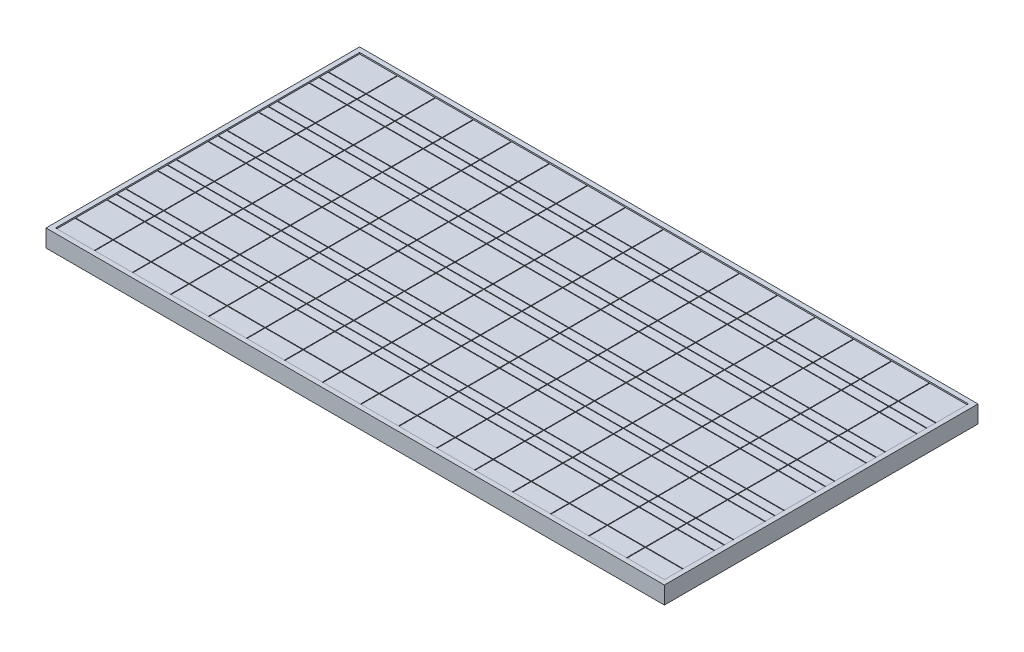
SolidWorks part; units mm, degrees
ref_plane "Front Plane" through (0, 0, 0) normal (0, 0, 1) x (1, 0, 0)
ref_plane "Top Plane" through (0, 0, 0) normal (0, 1, 0) x (1, 0, 0)
ref_plane "Right Plane" through (0, 0, 0) normal (1, 0, 0) x (0, 0, -1)
sketch "Sketch1" plane through (0, 0, 0) normal (0, 1, 0) x (1, 0, 0)
  line L1 (978, -496) -> (-978, -496)
  line L2 (978, -496) -> (978, 496)
  line L3 (978, 496) -> (-978, 496)
  line L4 (-978, -496) -> (-978, 496)
  line L5 (978, -496) -> (-978, 496) construction
  line L6 (978, 496) -> (-978, -496) construction
  line L11 (846.3925, -429.2543) -> (-845.4266, 428.7644) construction
  line L12 (846.3275, 428.1843) -> (-846.3275, -428.1843) construction
  point P0 (0, 0)
  point P6 (0, 0)
  dimension "D1" = 1956
  dimension "D2" = 992
extrude "Boss-Extrude1" add sketch "Sketch1" along normal blind 50
sketch "Sketch2" plane through (0, 0, 0) normal (0, -1, 0) x (1, 0, 0)
  line L14 (938, -456) -> (938, 456)
  line L15 (-938, -456) -> (938, -456)
  line L16 (-938, 456) -> (-938, -456)
  line L17 (938, 456) -> (-938, 456)
  line L18 (938, -456) -> (938, 456)
  line L19 (-938, -456) -> (938, -456)
  line L20 (-938, 456) -> (-938, -456)
  line L21 (938, 456) -> (-938, 456)
  dimension "D1" = 40
extrude "Cut-Extrude1" cut sketch "Sketch2" against normal blind 25
sketch "Sketch4" plane through (0, 50, 0) normal (0, 1, 0) x (1, 0, 0)
  line L13 (-963, 481) -> (-963, -481)
  line L14 (-963, -481) -> (963, -481)
  line L15 (963, -481) -> (963, 481)
  line L16 (963, 481) -> (-963, 481)
  line L17 (-963, 481) -> (-963, -481)
  line L18 (-963, -481) -> (963, -481)
  line L19 (963, -481) -> (963, 481)
  line L20 (963, 481) -> (-963, 481)
  line L21 (-978, 496) -> (-978, -496)
  line L22 (-978, -496) -> (978, -496)
  line L23 (978, -496) -> (978, 496)
  line L24 (978, 496) -> (-978, 496)
  line L25 (-978, 496) -> (-978, -496)
  line L26 (-978, -496) -> (978, -496)
  line L27 (978, -496) -> (978, 496)
  line L28 (978, 496) -> (-978, 496)
  dimension "D1" = 15
  dimension "D2" = 0
extrude "Boss-Extrude3" add sketch "Sketch4" along normal blind 5
sketch "Sketch5" plane through (0, 50, 0) normal (0, 1, 0) x (1, 0, 0)
  line L0 (-963, -481) -> (963, -481) construction
  line L1 (-961, -479) -> (-842.75, -479)
  line L2 (-961, -479) -> (-961, -421)
  line L3 (-961, -321) -> (-842.75, -321)
  line L4 (-842.75, -479) -> (-842.75, -421)
  line L5 (-963, 481) -> (-963, -481) construction
  line L6 (-961, -419) -> (-961, -321)
  line L7 (-961, -421) -> (-842.75, -421)
  line L9 (-961, -419) -> (-842.75, -419)
  line L11 (-842.75, -419) -> (-842.75, -321)
  line L12 (-961, -161) -> (-842.75, -161)
  line L13 (-842.75, -259) -> (-842.75, -161)
  line L14 (-961, -259) -> (-842.75, -259)
  line L15 (-961, -259) -> (-961, -161)
  line L16 (-961, -1) -> (-842.75, -1)
  line L17 (-842.75, -99) -> (-842.75, -1)
  line L18 (-961, -99) -> (-842.75, -99)
  line L19 (-961, -99) -> (-961, -1)
  line L20 (-961, 159) -> (-842.75, 159)
  line L21 (-842.75, 61) -> (-842.75, 159)
  line L22 (-961, 61) -> (-842.75, 61)
  line L23 (-961, 61) -> (-961, 159)
  line L24 (-961, 319) -> (-842.75, 319)
  line L25 (-842.75, 221) -> (-842.75, 319)
  line L26 (-961, 221) -> (-842.75, 221)
  line L27 (-961, 221) -> (-961, 319)
  line L28 (-961, 479) -> (-842.75, 479)
  line L29 (-842.75, 381) -> (-842.75, 479)
  line L30 (-961, 381) -> (-842.75, 381)
  line L31 (-961, 381) -> (-961, 479)
  line L32 (-961, -319) -> (-842.75, -319)
  line L33 (-842.75, -319) -> (-842.75, -290)
  line L34 (-961, -261) -> (-842.75, -261)
  line L35 (-961, -319) -> (-961, -290)
  line L36 (-961, -159) -> (-842.75, -159)
  line L37 (-842.75, -159) -> (-842.75, -130)
  line L38 (-961, -101) -> (-842.75, -101)
  line L39 (-961, -159) -> (-961, -130)
  line L40 (-961, 1) -> (-842.75, 1)
  line L41 (-842.75, 1) -> (-842.75, 30)
  line L42 (-961, 59) -> (-842.75, 59)
  line L43 (-961, 1) -> (-961, 30)
  line L44 (-961, 161) -> (-842.75, 161)
  line L45 (-842.75, 161) -> (-842.75, 190)
  line L46 (-961, 219) -> (-842.75, 219)
  line L47 (-961, 161) -> (-961, 190)
  line L48 (-961, 321) -> (-842.75, 321)
  line L49 (-842.75, 321) -> (-842.75, 350)
  line L50 (-961, 379) -> (-842.75, 379)
  line L51 (-961, 321) -> (-961, 350)
  line L53 (-961, -290) -> (-842.75, -290)
  line L55 (-961, -288) -> (-842.75, -288)
  line L57 (-961, -130) -> (-842.75, -130)
  line L59 (-961, -128) -> (-842.75, -128)
  line L61 (-961, 30) -> (-842.75, 30)
  line L63 (-961, 32) -> (-842.75, 32)
  line L65 (-961, 190) -> (-842.75, 190)
  line L67 (-961, 192) -> (-842.75, 192)
  line L69 (-961, 350) -> (-842.75, 350)
  line L71 (-961, 352) -> (-842.75, 352)
  line L72 (-961, -288) -> (-961, -261)
  line L73 (-842.75, -288) -> (-842.75, -261)
  line L74 (-961, -128) -> (-961, -101)
  line L75 (-842.75, -128) -> (-842.75, -101)
  line L76 (-961, 32) -> (-961, 59)
  line L77 (-842.75, 32) -> (-842.75, 59)
  line L78 (-961, 192) -> (-961, 219)
  line L79 (-842.75, 192) -> (-842.75, 219)
  line L80 (-961, 352) -> (-961, 379)
  line L81 (-842.75, 352) -> (-842.75, 379)
  line L82 (-840.75, -479) -> (-722.5, -479)
  line L83 (-722.5, -479) -> (-722.5, -421)
  line L84 (-840.75, -421) -> (-722.5, -421)
  line L85 (-840.75, -479) -> (-840.75, -421)
  line L86 (-840.75, -321) -> (-722.5, -321)
  line L87 (-722.5, -419) -> (-722.5, -321)
  line L88 (-840.75, -419) -> (-722.5, -419)
  line L89 (-840.75, -419) -> (-840.75, -321)
  line L90 (-840.75, -319) -> (-722.5, -319)
  line L91 (-722.5, -319) -> (-722.5, -290)
  line L92 (-840.75, -290) -> (-722.5, -290)
  line L93 (-840.75, -319) -> (-840.75, -290)
  line L94 (-840.75, -261) -> (-722.5, -261)
  line L95 (-722.5, -288) -> (-722.5, -261)
  line L96 (-840.75, -288) -> (-722.5, -288)
  line L97 (-840.75, -288) -> (-840.75, -261)
  line L98 (-840.75, -161) -> (-722.5, -161)
  line L99 (-722.5, -259) -> (-722.5, -161)
  line L100 (-840.75, -259) -> (-722.5, -259)
  line L101 (-840.75, -259) -> (-840.75, -161)
  line L102 (-840.75, -159) -> (-722.5, -159)
  line L103 (-722.5, -159) -> (-722.5, -130)
  line L104 (-840.75, -130) -> (-722.5, -130)
  line L105 (-840.75, -159) -> (-840.75, -130)
  line L106 (-840.75, -101) -> (-722.5, -101)
  line L107 (-722.5, -128) -> (-722.5, -101)
  line L108 (-840.75, -128) -> (-722.5, -128)
  line L109 (-840.75, -128) -> (-840.75, -101)
  line L110 (-840.75, -1) -> (-722.5, -1)
  line L111 (-722.5, -99) -> (-722.5, -1)
  line L112 (-840.75, -99) -> (-722.5, -99)
  line L113 (-840.75, -99) -> (-840.75, -1)
  line L114 (-840.75, 1) -> (-722.5, 1)
  line L115 (-722.5, 1) -> (-722.5, 30)
  line L116 (-840.75, 30) -> (-722.5, 30)
  line L117 (-840.75, 1) -> (-840.75, 30)
  line L118 (-840.75, 59) -> (-722.5, 59)
  line L119 (-722.5, 32) -> (-722.5, 59)
  line L120 (-840.75, 32) -> (-722.5, 32)
  line L121 (-840.75, 32) -> (-840.75, 59)
  line L122 (-840.75, 159) -> (-722.5, 159)
  line L123 (-722.5, 61) -> (-722.5, 159)
  line L124 (-840.75, 61) -> (-722.5, 61)
  line L125 (-840.75, 61) -> (-840.75, 159)
  line L126 (-840.75, 161) -> (-722.5, 161)
  line L127 (-722.5, 161) -> (-722.5, 190)
  line L128 (-840.75, 190) -> (-722.5, 190)
  line L129 (-840.75, 161) -> (-840.75, 190)
  line L130 (-840.75, 219) -> (-722.5, 219)
  line L131 (-722.5, 192) -> (-722.5, 219)
  line L132 (-840.75, 192) -> (-722.5, 192)
  line L133 (-840.75, 192) -> (-840.75, 219)
  line L134 (-840.75, 319) -> (-722.5, 319)
  line L135 (-722.5, 221) -> (-722.5, 319)
  line L136 (-840.75, 221) -> (-722.5, 221)
  line L137 (-840.75, 221) -> (-840.75, 319)
  line L138 (-840.75, 321) -> (-722.5, 321)
  line L139 (-722.5, 321) -> (-722.5, 350)
  line L140 (-840.75, 350) -> (-722.5, 350)
  line L141 (-840.75, 321) -> (-840.75, 350)
  line L142 (-840.75, 379) -> (-722.5, 379)
  line L143 (-722.5, 352) -> (-722.5, 379)
  line L144 (-840.75, 352) -> (-722.5, 352)
  line L145 (-840.75, 352) -> (-840.75, 379)
  line L146 (-840.75, 479) -> (-722.5, 479)
  line L147 (-722.5, 381) -> (-722.5, 479)
  line L148 (-840.75, 381) -> (-722.5, 381)
  line L149 (-840.75, 381) -> (-840.75, 479)
  line L150 (-720.5, -479) -> (-602.25, -479)
  line L151 (-602.25, -479) -> (-602.25, -421)
  line L152 (-720.5, -421) -> (-602.25, -421)
  line L153 (-720.5, -479) -> (-720.5, -421)
  line L154 (-720.5, -321) -> (-602.25, -321)
  line L155 (-602.25, -419) -> (-602.25, -321)
  line L156 (-720.5, -419) -> (-602.25, -419)
  line L157 (-720.5, -419) -> (-720.5, -321)
  line L158 (-720.5, -319) -> (-602.25, -319)
  line L159 (-602.25, -319) -> (-602.25, -290)
  line L160 (-720.5, -290) -> (-602.25, -290)
  line L161 (-720.5, -319) -> (-720.5, -290)
  line L162 (-720.5, -261) -> (-602.25, -261)
  line L163 (-602.25, -288) -> (-602.25, -261)
  line L164 (-720.5, -288) -> (-602.25, -288)
  line L165 (-720.5, -288) -> (-720.5, -261)
  line L166 (-720.5, -161) -> (-602.25, -161)
  line L167 (-602.25, -259) -> (-602.25, -161)
  line L168 (-720.5, -259) -> (-602.25, -259)
  line L169 (-720.5, -259) -> (-720.5, -161)
  line L170 (-720.5, -159) -> (-602.25, -159)
  line L171 (-602.25, -159) -> (-602.25, -130)
  line L172 (-720.5, -130) -> (-602.25, -130)
  line L173 (-720.5, -159) -> (-720.5, -130)
  line L174 (-720.5, -101) -> (-602.25, -101)
  line L175 (-602.25, -128) -> (-602.25, -101)
  line L176 (-720.5, -128) -> (-602.25, -128)
  line L177 (-720.5, -128) -> (-720.5, -101)
  line L178 (-720.5, -1) -> (-602.25, -1)
  line L179 (-602.25, -99) -> (-602.25, -1)
  line L180 (-720.5, -99) -> (-602.25, -99)
  line L181 (-720.5, -99) -> (-720.5, -1)
  line L182 (-720.5, 1) -> (-602.25, 1)
  line L183 (-602.25, 1) -> (-602.25, 30)
  line L184 (-720.5, 30) -> (-602.25, 30)
  line L185 (-720.5, 1) -> (-720.5, 30)
  line L186 (-720.5, 59) -> (-602.25, 59)
  line L187 (-602.25, 32) -> (-602.25, 59)
  line L188 (-720.5, 32) -> (-602.25, 32)
  line L189 (-720.5, 32) -> (-720.5, 59)
  line L190 (-720.5, 159) -> (-602.25, 159)
  line L191 (-602.25, 61) -> (-602.25, 159)
  line L192 (-720.5, 61) -> (-602.25, 61)
  line L193 (-720.5, 61) -> (-720.5, 159)
  line L194 (-720.5, 161) -> (-602.25, 161)
  line L195 (-602.25, 161) -> (-602.25, 190)
  line L196 (-720.5, 190) -> (-602.25, 190)
  line L197 (-720.5, 161) -> (-720.5, 190)
  line L198 (-720.5, 219) -> (-602.25, 219)
  line L199 (-602.25, 192) -> (-602.25, 219)
  line L200 (-720.5, 192) -> (-602.25, 192)
  line L201 (-720.5, 192) -> (-720.5, 219)
  line L202 (-720.5, 319) -> (-602.25, 319)
  line L203 (-602.25, 221) -> (-602.25, 319)
  line L204 (-720.5, 221) -> (-602.25, 221)
  line L205 (-720.5, 221) -> (-720.5, 319)
  line L206 (-720.5, 321) -> (-602.25, 321)
  line L207 (-602.25, 321) -> (-602.25, 350)
  line L208 (-720.5, 350) -> (-602.25, 350)
  line L209 (-720.5, 321) -> (-720.5, 350)
  line L210 (-720.5, 379) -> (-602.25, 379)
  line L211 (-602.25, 352) -> (-602.25, 379)
  line L212 (-720.5, 352) -> (-602.25, 352)
  line L213 (-720.5, 352) -> (-720.5, 379)
  line L214 (-720.5, 479) -> (-602.25, 479)
  line L215 (-602.25, 381) -> (-602.25, 479)
  line L216 (-720.5, 381) -> (-602.25, 381)
  line L217 (-720.5, 381) -> (-720.5, 479)
  line L218 (-600.25, -479) -> (-482, -479)
  line L219 (-482, -479) -> (-482, -421)
  line L220 (-600.25, -421) -> (-482, -421)
  line L221 (-600.25, -479) -> (-600.25, -421)
  line L222 (-600.25, -321) -> (-482, -321)
  line L223 (-482, -419) -> (-482, -321)
  line L224 (-600.25, -419) -> (-482, -419)
  line L225 (-600.25, -419) -> (-600.25, -321)
  line L226 (-600.25, -319) -> (-482, -319)
  line L227 (-482, -319) -> (-482, -290)
  line L228 (-600.25, -290) -> (-482, -290)
  line L229 (-600.25, -319) -> (-600.25, -290)
  line L230 (-600.25, -261) -> (-482, -261)
  line L231 (-482, -288) -> (-482, -261)
  line L232 (-600.25, -288) -> (-482, -288)
  line L233 (-600.25, -288) -> (-600.25, -261)
  line L234 (-600.25, -161) -> (-482, -161)
  line L235 (-482, -259) -> (-482, -161)
  line L236 (-600.25, -259) -> (-482, -259)
  line L237 (-600.25, -259) -> (-600.25, -161)
  line L238 (-600.25, -159) -> (-482, -159)
  line L239 (-482, -159) -> (-482, -130)
  line L240 (-600.25, -130) -> (-482, -130)
  line L241 (-600.25, -159) -> (-600.25, -130)
  line L242 (-600.25, -101) -> (-482, -101)
  line L243 (-482, -128) -> (-482, -101)
  line L244 (-600.25, -128) -> (-482, -128)
  line L245 (-600.25, -128) -> (-600.25, -101)
  line L246 (-600.25, -1) -> (-482, -1)
  line L247 (-482, -99) -> (-482, -1)
  line L248 (-600.25, -99) -> (-482, -99)
  line L249 (-600.25, -99) -> (-600.25, -1)
  line L250 (-600.25, 1) -> (-482, 1)
  line L251 (-482, 1) -> (-482, 30)
  line L252 (-600.25, 30) -> (-482, 30)
  line L253 (-600.25, 1) -> (-600.25, 30)
  line L254 (-600.25, 59) -> (-482, 59)
  line L255 (-482, 32) -> (-482, 59)
  line L256 (-600.25, 32) -> (-482, 32)
  line L257 (-600.25, 32) -> (-600.25, 59)
  line L258 (-600.25, 159) -> (-482, 159)
  line L259 (-482, 61) -> (-482, 159)
  line L260 (-600.25, 61) -> (-482, 61)
  line L261 (-600.25, 61) -> (-600.25, 159)
  line L262 (-600.25, 161) -> (-482, 161)
  line L263 (-482, 161) -> (-482, 190)
  line L264 (-600.25, 190) -> (-482, 190)
  line L265 (-600.25, 161) -> (-600.25, 190)
  line L266 (-600.25, 219) -> (-482, 219)
  line L267 (-482, 192) -> (-482, 219)
  line L268 (-600.25, 192) -> (-482, 192)
  line L269 (-600.25, 192) -> (-600.25, 219)
  line L270 (-600.25, 319) -> (-482, 319)
  line L271 (-482, 221) -> (-482, 319)
  line L272 (-600.25, 221) -> (-482, 221)
  line L273 (-600.25, 221) -> (-600.25, 319)
  line L274 (-600.25, 321) -> (-482, 321)
  line L275 (-482, 321) -> (-482, 350)
  line L276 (-600.25, 350) -> (-482, 350)
  line L277 (-600.25, 321) -> (-600.25, 350)
  line L278 (-600.25, 379) -> (-482, 379)
  line L279 (-482, 352) -> (-482, 379)
  line L280 (-600.25, 352) -> (-482, 352)
  line L281 (-600.25, 352) -> (-600.25, 379)
  line L282 (-600.25, 479) -> (-482, 479)
  line L283 (-482, 381) -> (-482, 479)
  line L284 (-600.25, 381) -> (-482, 381)
  line L285 (-600.25, 381) -> (-600.25, 479)
  line L286 (-480, -479) -> (-361.75, -479)
  line L287 (-361.75, -479) -> (-361.75, -421)
  line L288 (-480, -421) -> (-361.75, -421)
  line L289 (-480, -479) -> (-480, -421)
  line L290 (-480, -321) -> (-361.75, -321)
  line L291 (-361.75, -419) -> (-361.75, -321)
  line L292 (-480, -419) -> (-361.75, -419)
  line L293 (-480, -419) -> (-480, -321)
  line L294 (-480, -319) -> (-361.75, -319)
  line L295 (-361.75, -319) -> (-361.75, -290)
  line L296 (-480, -290) -> (-361.75, -290)
  line L297 (-480, -319) -> (-480, -290)
  line L298 (-480, -261) -> (-361.75, -261)
  line L299 (-361.75, -288) -> (-361.75, -261)
  line L300 (-480, -288) -> (-361.75, -288)
  line L301 (-480, -288) -> (-480, -261)
  line L302 (-480, -161) -> (-361.75, -161)
  line L303 (-361.75, -259) -> (-361.75, -161)
  line L304 (-480, -259) -> (-361.75, -259)
  line L305 (-480, -259) -> (-480, -161)
  line L306 (-480, -159) -> (-361.75, -159)
  line L307 (-361.75, -159) -> (-361.75, -130)
  line L308 (-480, -130) -> (-361.75, -130)
  line L309 (-480, -159) -> (-480, -130)
  line L310 (-480, -101) -> (-361.75, -101)
  line L311 (-361.75, -128) -> (-361.75, -101)
  line L312 (-480, -128) -> (-361.75, -128)
  line L313 (-480, -128) -> (-480, -101)
  line L314 (-480, -1) -> (-361.75, -1)
  line L315 (-361.75, -99) -> (-361.75, -1)
  line L316 (-480, -99) -> (-361.75, -99)
  line L317 (-480, -99) -> (-480, -1)
  line L318 (-480, 1) -> (-361.75, 1)
  line L319 (-361.75, 1) -> (-361.75, 30)
  line L320 (-480, 30) -> (-361.75, 30)
  line L321 (-480, 1) -> (-480, 30)
  line L322 (-480, 59) -> (-361.75, 59)
  line L323 (-361.75, 32) -> (-361.75, 59)
  line L324 (-480, 32) -> (-361.75, 32)
  line L325 (-480, 32) -> (-480, 59)
  line L326 (-480, 159) -> (-361.75, 159)
  line L327 (-361.75, 61) -> (-361.75, 159)
  line L328 (-480, 61) -> (-361.75, 61)
  line L329 (-480, 61) -> (-480, 159)
  line L330 (-480, 161) -> (-361.75, 161)
  line L331 (-361.75, 161) -> (-361.75, 190)
  line L332 (-480, 190) -> (-361.75, 190)
  line L333 (-480, 161) -> (-480, 190)
  line L334 (-480, 219) -> (-361.75, 219)
  line L335 (-361.75, 192) -> (-361.75, 219)
  line L336 (-480, 192) -> (-361.75, 192)
  line L337 (-480, 192) -> (-480, 219)
  line L338 (-480, 319) -> (-361.75, 319)
  line L339 (-361.75, 221) -> (-361.75, 319)
  line L340 (-480, 221) -> (-361.75, 221)
  line L341 (-480, 221) -> (-480, 319)
  line L342 (-480, 321) -> (-361.75, 321)
  line L343 (-361.75, 321) -> (-361.75, 350)
  line L344 (-480, 350) -> (-361.75, 350)
  line L345 (-480, 321) -> (-480, 350)
  line L346 (-480, 379) -> (-361.75, 379)
  line L347 (-361.75, 352) -> (-361.75, 379)
  line L348 (-480, 352) -> (-361.75, 352)
  line L349 (-480, 352) -> (-480, 379)
  line L350 (-480, 479) -> (-361.75, 479)
  line L351 (-361.75, 381) -> (-361.75, 479)
  line L352 (-480, 381) -> (-361.75, 381)
  line L353 (-480, 381) -> (-480, 479)
  line L354 (-359.75, -479) -> (-241.5, -479)
  line L355 (-241.5, -479) -> (-241.5, -421)
  line L356 (-359.75, -421) -> (-241.5, -421)
  line L357 (-359.75, -479) -> (-359.75, -421)
  line L358 (-359.75, -321) -> (-241.5, -321)
  line L359 (-241.5, -419) -> (-241.5, -321)
  line L360 (-359.75, -419) -> (-241.5, -419)
  line L361 (-359.75, -419) -> (-359.75, -321)
  line L362 (-359.75, -319) -> (-241.5, -319)
  line L363 (-241.5, -319) -> (-241.5, -290)
  line L364 (-359.75, -290) -> (-241.5, -290)
  line L365 (-359.75, -319) -> (-359.75, -290)
  line L366 (-359.75, -261) -> (-241.5, -261)
  line L367 (-241.5, -288) -> (-241.5, -261)
  line L368 (-359.75, -288) -> (-241.5, -288)
  line L369 (-359.75, -288) -> (-359.75, -261)
  line L370 (-359.75, -161) -> (-241.5, -161)
  line L371 (-241.5, -259) -> (-241.5, -161)
  line L372 (-359.75, -259) -> (-241.5, -259)
  line L373 (-359.75, -259) -> (-359.75, -161)
  line L374 (-359.75, -159) -> (-241.5, -159)
  line L375 (-241.5, -159) -> (-241.5, -130)
  line L376 (-359.75, -130) -> (-241.5, -130)
  line L377 (-359.75, -159) -> (-359.75, -130)
  line L378 (-359.75, -101) -> (-241.5, -101)
  line L379 (-241.5, -128) -> (-241.5, -101)
  line L380 (-359.75, -128) -> (-241.5, -128)
  line L381 (-359.75, -128) -> (-359.75, -101)
  line L382 (-359.75, -1) -> (-241.5, -1)
  line L383 (-241.5, -99) -> (-241.5, -1)
  line L384 (-359.75, -99) -> (-241.5, -99)
  line L385 (-359.75, -99) -> (-359.75, -1)
  line L386 (-359.75, 1) -> (-241.5, 1)
  line L387 (-241.5, 1) -> (-241.5, 30)
  line L388 (-359.75, 30) -> (-241.5, 30)
  line L389 (-359.75, 1) -> (-359.75, 30)
  line L390 (-359.75, 59) -> (-241.5, 59)
  line L391 (-241.5, 32) -> (-241.5, 59)
  line L392 (-359.75, 32) -> (-241.5, 32)
  line L393 (-359.75, 32) -> (-359.75, 59)
  line L394 (-359.75, 159) -> (-241.5, 159)
  line L395 (-241.5, 61) -> (-241.5, 159)
  line L396 (-359.75, 61) -> (-241.5, 61)
  line L397 (-359.75, 61) -> (-359.75, 159)
  line L398 (-359.75, 161) -> (-241.5, 161)
  line L399 (-241.5, 161) -> (-241.5, 190)
  line L400 (-359.75, 190) -> (-241.5, 190)
  line L401 (-359.75, 161) -> (-359.75, 190)
  line L402 (-359.75, 219) -> (-241.5, 219)
  line L403 (-241.5, 192) -> (-241.5, 219)
  line L404 (-359.75, 192) -> (-241.5, 192)
  line L405 (-359.75, 192) -> (-359.75, 219)
  line L406 (-359.75, 319) -> (-241.5, 319)
  line L407 (-241.5, 221) -> (-241.5, 319)
  line L408 (-359.75, 221) -> (-241.5, 221)
  line L409 (-359.75, 221) -> (-359.75, 319)
  line L410 (-359.75, 321) -> (-241.5, 321)
  line L411 (-241.5, 321) -> (-241.5, 350)
  line L412 (-359.75, 350) -> (-241.5, 350)
  line L413 (-359.75, 321) -> (-359.75, 350)
  line L414 (-359.75, 379) -> (-241.5, 379)
  line L415 (-241.5, 352) -> (-241.5, 379)
  line L416 (-359.75, 352) -> (-241.5, 352)
  line L417 (-359.75, 352) -> (-359.75, 379)
  line L418 (-359.75, 479) -> (-241.5, 479)
  line L419 (-241.5, 381) -> (-241.5, 479)
  line L420 (-359.75, 381) -> (-241.5, 381)
  line L421 (-359.75, 381) -> (-359.75, 479)
  line L422 (-239.5, -479) -> (-121.25, -479)
  line L423 (-121.25, -479) -> (-121.25, -421)
  line L424 (-239.5, -421) -> (-121.25, -421)
  line L425 (-239.5, -479) -> (-239.5, -421)
  line L426 (-239.5, -321) -> (-121.25, -321)
  line L427 (-121.25, -419) -> (-121.25, -321)
  line L428 (-239.5, -419) -> (-121.25, -419)
  line L429 (-239.5, -419) -> (-239.5, -321)
  line L430 (-239.5, -319) -> (-121.25, -319)
  line L431 (-121.25, -319) -> (-121.25, -290)
  line L432 (-239.5, -290) -> (-121.25, -290)
  line L433 (-239.5, -319) -> (-239.5, -290)
  line L434 (-239.5, -261) -> (-121.25, -261)
  line L435 (-121.25, -288) -> (-121.25, -261)
  line L436 (-239.5, -288) -> (-121.25, -288)
  line L437 (-239.5, -288) -> (-239.5, -261)
  line L438 (-239.5, -161) -> (-121.25, -161)
  line L439 (-121.25, -259) -> (-121.25, -161)
  line L440 (-239.5, -259) -> (-121.25, -259)
  line L441 (-239.5, -259) -> (-239.5, -161)
  line L442 (-239.5, -159) -> (-121.25, -159)
  line L443 (-121.25, -159) -> (-121.25, -130)
  line L444 (-239.5, -130) -> (-121.25, -130)
  line L445 (-239.5, -159) -> (-239.5, -130)
  line L446 (-239.5, -101) -> (-121.25, -101)
  line L447 (-121.25, -128) -> (-121.25, -101)
  line L448 (-239.5, -128) -> (-121.25, -128)
  line L449 (-239.5, -128) -> (-239.5, -101)
  line L450 (-239.5, -1) -> (-121.25, -1)
  line L451 (-121.25, -99) -> (-121.25, -1)
  line L452 (-239.5, -99) -> (-121.25, -99)
  line L453 (-239.5, -99) -> (-239.5, -1)
  line L454 (-239.5, 1) -> (-121.25, 1)
  line L455 (-121.25, 1) -> (-121.25, 30)
  line L456 (-239.5, 30) -> (-121.25, 30)
  line L457 (-239.5, 1) -> (-239.5, 30)
  line L458 (-239.5, 59) -> (-121.25, 59)
  line L459 (-121.25, 32) -> (-121.25, 59)
  line L460 (-239.5, 32) -> (-121.25, 32)
  line L461 (-239.5, 32) -> (-239.5, 59)
  line L462 (-239.5, 159) -> (-121.25, 159)
  line L463 (-121.25, 61) -> (-121.25, 159)
  line L464 (-239.5, 61) -> (-121.25, 61)
  line L465 (-239.5, 61) -> (-239.5, 159)
  line L466 (-239.5, 161) -> (-121.25, 161)
  line L467 (-121.25, 161) -> (-121.25, 190)
  line L468 (-239.5, 190) -> (-121.25, 190)
  line L469 (-239.5, 161) -> (-239.5, 190)
  line L470 (-239.5, 219) -> (-121.25, 219)
  line L471 (-121.25, 192) -> (-121.25, 219)
  line L472 (-239.5, 192) -> (-121.25, 192)
  line L473 (-239.5, 192) -> (-239.5, 219)
  line L474 (-239.5, 319) -> (-121.25, 319)
  line L475 (-121.25, 221) -> (-121.25, 319)
  line L476 (-239.5, 221) -> (-121.25, 221)
  line L477 (-239.5, 221) -> (-239.5, 319)
  line L478 (-239.5, 321) -> (-121.25, 321)
  line L479 (-121.25, 321) -> (-121.25, 350)
  line L480 (-239.5, 350) -> (-121.25, 350)
  line L481 (-239.5, 321) -> (-239.5, 350)
  line L482 (-239.5, 379) -> (-121.25, 379)
  line L483 (-121.25, 352) -> (-121.25, 379)
  line L484 (-239.5, 352) -> (-121.25, 352)
  line L485 (-239.5, 352) -> (-239.5, 379)
  line L486 (-239.5, 479) -> (-121.25, 479)
  line L487 (-121.25, 381) -> (-121.25, 479)
  line L488 (-239.5, 381) -> (-121.25, 381)
  line L489 (-239.5, 381) -> (-239.5, 479)
  line L490 (-119.25, -479) -> (-1, -479)
  line L491 (-1, -479) -> (-1, -421)
  line L492 (-119.25, -421) -> (-1, -421)
  line L493 (-119.25, -479) -> (-119.25, -421)
  line L494 (-119.25, -321) -> (-1, -321)
  line L495 (-1, -419) -> (-1, -321)
  line L496 (-119.25, -419) -> (-1, -419)
  line L497 (-119.25, -419) -> (-119.25, -321)
  line L498 (-119.25, -319) -> (-1, -319)
  line L499 (-1, -319) -> (-1, -290)
  line L500 (-119.25, -290) -> (-1, -290)
  line L501 (-119.25, -319) -> (-119.25, -290)
  line L502 (-119.25, -261) -> (-1, -261)
  line L503 (-1, -288) -> (-1, -261)
  line L504 (-119.25, -288) -> (-1, -288)
  line L505 (-119.25, -288) -> (-119.25, -261)
  line L506 (-119.25, -161) -> (-1, -161)
  line L507 (-1, -259) -> (-1, -161)
  line L508 (-119.25, -259) -> (-1, -259)
  line L509 (-119.25, -259) -> (-119.25, -161)
  line L510 (-119.25, -159) -> (-1, -159)
  line L511 (-1, -159) -> (-1, -130)
  line L512 (-119.25, -130) -> (-1, -130)
  line L513 (-119.25, -159) -> (-119.25, -130)
  line L514 (-119.25, -101) -> (-1, -101)
  line L515 (-1, -128) -> (-1, -101)
  line L516 (-119.25, -128) -> (-1, -128)
  line L517 (-119.25, -128) -> (-119.25, -101)
  line L518 (-119.25, -1) -> (-1, -1)
  line L519 (-1, -99) -> (-1, -1)
  line L520 (-119.25, -99) -> (-1, -99)
  line L521 (-119.25, -99) -> (-119.25, -1)
  line L522 (-119.25, 1) -> (-1, 1)
  line L523 (-1, 1) -> (-1, 30)
  line L524 (-119.25, 30) -> (-1, 30)
  line L525 (-119.25, 1) -> (-119.25, 30)
  line L526 (-119.25, 59) -> (-1, 59)
  line L527 (-1, 32) -> (-1, 59)
  line L528 (-119.25, 32) -> (-1, 32)
  line L529 (-119.25, 32) -> (-119.25, 59)
  line L530 (-119.25, 159) -> (-1, 159)
  line L531 (-1, 61) -> (-1, 159)
  line L532 (-119.25, 61) -> (-1, 61)
  line L533 (-119.25, 61) -> (-119.25, 159)
  line L534 (-119.25, 161) -> (-1, 161)
  line L535 (-1, 161) -> (-1, 190)
  line L536 (-119.25, 190) -> (-1, 190)
  line L537 (-119.25, 161) -> (-119.25, 190)
  line L538 (-119.25, 219) -> (-1, 219)
  line L539 (-1, 192) -> (-1, 219)
  line L540 (-119.25, 192) -> (-1, 192)
  line L541 (-119.25, 192) -> (-119.25, 219)
  line L542 (-119.25, 319) -> (-1, 319)
  line L543 (-1, 221) -> (-1, 319)
  line L544 (-119.25, 221) -> (-1, 221)
  line L545 (-119.25, 221) -> (-119.25, 319)
  line L546 (-119.25, 321) -> (-1, 321)
  line L547 (-1, 321) -> (-1, 350)
  line L548 (-119.25, 350) -> (-1, 350)
  line L549 (-119.25, 321) -> (-119.25, 350)
  line L550 (-119.25, 379) -> (-1, 379)
  line L551 (-1, 352) -> (-1, 379)
  line L552 (-119.25, 352) -> (-1, 352)
  line L553 (-119.25, 352) -> (-119.25, 379)
  line L554 (-119.25, 479) -> (-1, 479)
  line L555 (-1, 381) -> (-1, 479)
  line L556 (-119.25, 381) -> (-1, 381)
  line L557 (-119.25, 381) -> (-119.25, 479)
  line L558 (1, -479) -> (119.25, -479)
  line L559 (119.25, -479) -> (119.25, -421)
  line L560 (1, -421) -> (119.25, -421)
  line L561 (1, -479) -> (1, -421)
  line L562 (1, -321) -> (119.25, -321)
  line L563 (119.25, -419) -> (119.25, -321)
  line L564 (1, -419) -> (119.25, -419)
  line L565 (1, -419) -> (1, -321)
  line L566 (1, -319) -> (119.25, -319)
  line L567 (119.25, -319) -> (119.25, -290)
  line L568 (1, -290) -> (119.25, -290)
  line L569 (1, -319) -> (1, -290)
  line L570 (1, -261) -> (119.25, -261)
  line L571 (119.25, -288) -> (119.25, -261)
  line L572 (1, -288) -> (119.25, -288)
  line L573 (1, -288) -> (1, -261)
  line L574 (1, -161) -> (119.25, -161)
  line L575 (119.25, -259) -> (119.25, -161)
  line L576 (1, -259) -> (119.25, -259)
  line L577 (1, -259) -> (1, -161)
  line L578 (1, -159) -> (119.25, -159)
  line L579 (119.25, -159) -> (119.25, -130)
  line L580 (1, -130) -> (119.25, -130)
  line L581 (1, -159) -> (1, -130)
  line L582 (1, -101) -> (119.25, -101)
  line L583 (119.25, -128) -> (119.25, -101)
  line L584 (1, -128) -> (119.25, -128)
  line L585 (1, -128) -> (1, -101)
  line L586 (1, -1) -> (119.25, -1)
  line L587 (119.25, -99) -> (119.25, -1)
  line L588 (1, -99) -> (119.25, -99)
  line L589 (1, -99) -> (1, -1)
  line L590 (1, 1) -> (119.25, 1)
  line L591 (119.25, 1) -> (119.25, 30)
  line L592 (1, 30) -> (119.25, 30)
  line L593 (1, 1) -> (1, 30)
  line L594 (1, 59) -> (119.25, 59)
  line L595 (119.25, 32) -> (119.25, 59)
  line L596 (1, 32) -> (119.25, 32)
  line L597 (1, 32) -> (1, 59)
  line L598 (1, 159) -> (119.25, 159)
  line L599 (119.25, 61) -> (119.25, 159)
  line L600 (1, 61) -> (119.25, 61)
  line L601 (1, 61) -> (1, 159)
  line L602 (1, 161) -> (119.25, 161)
  line L603 (119.25, 161) -> (119.25, 190)
  line L604 (1, 190) -> (119.25, 190)
  line L605 (1, 161) -> (1, 190)
  line L606 (1, 219) -> (119.25, 219)
  line L607 (119.25, 192) -> (119.25, 219)
  line L608 (1, 192) -> (119.25, 192)
  line L609 (1, 192) -> (1, 219)
  line L610 (1, 319) -> (119.25, 319)
  line L611 (119.25, 221) -> (119.25, 319)
  line L612 (1, 221) -> (119.25, 221)
  line L613 (1, 221) -> (1, 319)
  line L614 (1, 321) -> (119.25, 321)
  line L615 (119.25, 321) -> (119.25, 350)
  line L616 (1, 350) -> (119.25, 350)
  line L617 (1, 321) -> (1, 350)
  line L618 (1, 379) -> (119.25, 379)
  line L619 (119.25, 352) -> (119.25, 379)
  line L620 (1, 352) -> (119.25, 352)
  line L621 (1, 352) -> (1, 379)
  line L622 (1, 479) -> (119.25, 479)
  line L623 (119.25, 381) -> (119.25, 479)
  line L624 (1, 381) -> (119.25, 381)
  line L625 (1, 381) -> (1, 479)
  line L626 (121.25, -479) -> (239.5, -479)
  line L627 (239.5, -479) -> (239.5, -421)
  line L628 (121.25, -421) -> (239.5, -421)
  line L629 (121.25, -479) -> (121.25, -421)
  line L630 (121.25, -321) -> (239.5, -321)
  line L631 (239.5, -419) -> (239.5, -321)
  line L632 (121.25, -419) -> (239.5, -419)
  line L633 (121.25, -419) -> (121.25, -321)
  line L634 (121.25, -319) -> (239.5, -319)
  line L635 (239.5, -319) -> (239.5, -290)
  line L636 (121.25, -290) -> (239.5, -290)
  line L637 (121.25, -319) -> (121.25, -290)
  line L638 (121.25, -261) -> (239.5, -261)
  line L639 (239.5, -288) -> (239.5, -261)
  line L640 (121.25, -288) -> (239.5, -288)
  line L641 (121.25, -288) -> (121.25, -261)
  line L642 (121.25, -161) -> (239.5, -161)
  line L643 (239.5, -259) -> (239.5, -161)
  line L644 (121.25, -259) -> (239.5, -259)
  line L645 (121.25, -259) -> (121.25, -161)
  line L646 (121.25, -159) -> (239.5, -159)
  line L647 (239.5, -159) -> (239.5, -130)
  line L648 (121.25, -130) -> (239.5, -130)
  line L649 (121.25, -159) -> (121.25, -130)
  line L650 (121.25, -101) -> (239.5, -101)
  line L651 (239.5, -128) -> (239.5, -101)
  line L652 (121.25, -128) -> (239.5, -128)
  line L653 (121.25, -128) -> (121.25, -101)
  line L654 (121.25, -1) -> (239.5, -1)
  line L655 (239.5, -99) -> (239.5, -1)
  line L656 (121.25, -99) -> (239.5, -99)
  line L657 (121.25, -99) -> (121.25, -1)
  line L658 (121.25, 1) -> (239.5, 1)
  line L659 (239.5, 1) -> (239.5, 30)
  line L660 (121.25, 30) -> (239.5, 30)
  line L661 (121.25, 1) -> (121.25, 30)
  line L662 (121.25, 59) -> (239.5, 59)
  line L663 (239.5, 32) -> (239.5, 59)
  line L664 (121.25, 32) -> (239.5, 32)
  line L665 (121.25, 32) -> (121.25, 59)
  line L666 (121.25, 159) -> (239.5, 159)
  line L667 (239.5, 61) -> (239.5, 159)
  line L668 (121.25, 61) -> (239.5, 61)
  line L669 (121.25, 61) -> (121.25, 159)
  line L670 (121.25, 161) -> (239.5, 161)
  line L671 (239.5, 161) -> (239.5, 190)
  line L672 (121.25, 190) -> (239.5, 190)
  line L673 (121.25, 161) -> (121.25, 190)
  line L674 (121.25, 219) -> (239.5, 219)
  line L675 (239.5, 192) -> (239.5, 219)
  line L676 (121.25, 192) -> (239.5, 192)
  line L677 (121.25, 192) -> (121.25, 219)
  line L678 (121.25, 319) -> (239.5, 319)
  line L679 (239.5, 221) -> (239.5, 319)
  line L680 (121.25, 221) -> (239.5, 221)
  line L681 (121.25, 221) -> (121.25, 319)
  line L682 (121.25, 321) -> (239.5, 321)
  line L683 (239.5, 321) -> (239.5, 350)
  line L684 (121.25, 350) -> (239.5, 350)
  line L685 (121.25, 321) -> (121.25, 350)
  line L686 (121.25, 379) -> (239.5, 379)
  line L687 (239.5, 352) -> (239.5, 379)
  line L688 (121.25, 352) -> (239.5, 352)
  line L689 (121.25, 352) -> (121.25, 379)
  line L690 (121.25, 479) -> (239.5, 479)
  line L691 (239.5, 381) -> (239.5, 479)
  line L692 (121.25, 381) -> (239.5, 381)
  line L693 (121.25, 381) -> (121.25, 479)
  line L694 (241.5, -479) -> (359.75, -479)
  line L695 (359.75, -479) -> (359.75, -421)
  line L696 (241.5, -421) -> (359.75, -421)
  line L697 (241.5, -479) -> (241.5, -421)
  line L698 (241.5, -321) -> (359.75, -321)
  line L699 (359.75, -419) -> (359.75, -321)
  line L700 (241.5, -419) -> (359.75, -419)
  line L701 (241.5, -419) -> (241.5, -321)
  line L702 (241.5, -319) -> (359.75, -319)
  line L703 (359.75, -319) -> (359.75, -290)
  line L704 (241.5, -290) -> (359.75, -290)
  line L705 (241.5, -319) -> (241.5, -290)
  line L706 (241.5, -261) -> (359.75, -261)
  line L707 (359.75, -288) -> (359.75, -261)
  line L708 (241.5, -288) -> (359.75, -288)
  line L709 (241.5, -288) -> (241.5, -261)
  line L710 (241.5, -161) -> (359.75, -161)
  line L711 (359.75, -259) -> (359.75, -161)
  line L712 (241.5, -259) -> (359.75, -259)
  line L713 (241.5, -259) -> (241.5, -161)
  line L714 (241.5, -159) -> (359.75, -159)
  line L715 (359.75, -159) -> (359.75, -130)
  line L716 (241.5, -130) -> (359.75, -130)
  line L717 (241.5, -159) -> (241.5, -130)
  line L718 (241.5, -101) -> (359.75, -101)
  line L719 (359.75, -128) -> (359.75, -101)
  line L720 (241.5, -128) -> (359.75, -128)
  line L721 (241.5, -128) -> (241.5, -101)
  line L722 (241.5, -1) -> (359.75, -1)
  line L723 (359.75, -99) -> (359.75, -1)
  line L724 (241.5, -99) -> (359.75, -99)
  line L725 (241.5, -99) -> (241.5, -1)
  line L726 (241.5, 1) -> (359.75, 1)
  line L727 (359.75, 1) -> (359.75, 30)
  line L728 (241.5, 30) -> (359.75, 30)
  line L729 (241.5, 1) -> (241.5, 30)
  line L730 (241.5, 59) -> (359.75, 59)
  line L731 (359.75, 32) -> (359.75, 59)
  line L732 (241.5, 32) -> (359.75, 32)
  line L733 (241.5, 32) -> (241.5, 59)
  line L734 (241.5, 159) -> (359.75, 159)
  line L735 (359.75, 61) -> (359.75, 159)
  line L736 (241.5, 61) -> (359.75, 61)
  line L737 (241.5, 61) -> (241.5, 159)
  line L738 (241.5, 161) -> (359.75, 161)
  line L739 (359.75, 161) -> (359.75, 190)
  line L740 (241.5, 190) -> (359.75, 190)
  line L741 (241.5, 161) -> (241.5, 190)
  line L742 (241.5, 219) -> (359.75, 219)
  line L743 (359.75, 192) -> (359.75, 219)
  line L744 (241.5, 192) -> (359.75, 192)
  line L745 (241.5, 192) -> (241.5, 219)
  line L746 (241.5, 319) -> (359.75, 319)
  line L747 (359.75, 221) -> (359.75, 319)
  line L748 (241.5, 221) -> (359.75, 221)
  line L749 (241.5, 221) -> (241.5, 319)
  line L750 (241.5, 321) -> (359.75, 321)
  line L751 (359.75, 321) -> (359.75, 350)
  line L752 (241.5, 350) -> (359.75, 350)
  line L753 (241.5, 321) -> (241.5, 350)
  line L754 (241.5, 379) -> (359.75, 379)
  line L755 (359.75, 352) -> (359.75, 379)
  line L756 (241.5, 352) -> (359.75, 352)
  line L757 (241.5, 352) -> (241.5, 379)
  line L758 (241.5, 479) -> (359.75, 479)
  line L759 (359.75, 381) -> (359.75, 479)
  line L760 (241.5, 381) -> (359.75, 381)
  line L761 (241.5, 381) -> (241.5, 479)
  line L762 (361.75, -479) -> (480, -479)
  line L763 (480, -479) -> (480, -421)
  line L764 (361.75, -421) -> (480, -421)
  line L765 (361.75, -479) -> (361.75, -421)
  line L766 (361.75, -321) -> (480, -321)
  line L767 (480, -419) -> (480, -321)
  line L768 (361.75, -419) -> (480, -419)
  line L769 (361.75, -419) -> (361.75, -321)
  line L770 (361.75, -319) -> (480, -319)
  line L771 (480, -319) -> (480, -290)
  line L772 (361.75, -290) -> (480, -290)
  line L773 (361.75, -319) -> (361.75, -290)
  line L774 (361.75, -261) -> (480, -261)
  line L775 (480, -288) -> (480, -261)
  line L776 (361.75, -288) -> (480, -288)
  line L777 (361.75, -288) -> (361.75, -261)
  line L778 (361.75, -161) -> (480, -161)
  line L779 (480, -259) -> (480, -161)
  line L780 (361.75, -259) -> (480, -259)
  line L781 (361.75, -259) -> (361.75, -161)
  line L782 (361.75, -159) -> (480, -159)
  line L783 (480, -159) -> (480, -130)
  line L784 (361.75, -130) -> (480, -130)
  line L785 (361.75, -159) -> (361.75, -130)
  line L786 (361.75, -101) -> (480, -101)
  line L787 (480, -128) -> (480, -101)
  line L788 (361.75, -128) -> (480, -128)
  line L789 (361.75, -128) -> (361.75, -101)
  line L790 (361.75, -1) -> (480, -1)
  line L791 (480, -99) -> (480, -1)
  line L792 (361.75, -99) -> (480, -99)
  line L793 (361.75, -99) -> (361.75, -1)
  line L794 (361.75, 1) -> (480, 1)
  line L795 (480, 1) -> (480, 30)
  line L796 (361.75, 30) -> (480, 30)
  line L797 (361.75, 1) -> (361.75, 30)
  line L798 (361.75, 59) -> (480, 59)
  line L799 (480, 32) -> (480, 59)
  line L800 (361.75, 32) -> (480, 32)
  line L801 (361.75, 32) -> (361.75, 59)
  line L802 (361.75, 159) -> (480, 159)
  line L803 (480, 61) -> (480, 159)
  line L804 (361.75, 61) -> (480, 61)
  line L805 (361.75, 61) -> (361.75, 159)
  line L806 (361.75, 161) -> (480, 161)
  line L807 (480, 161) -> (480, 190)
  line L808 (361.75, 190) -> (480, 190)
  line L809 (361.75, 161) -> (361.75, 190)
  line L810 (361.75, 219) -> (480, 219)
  line L811 (480, 192) -> (480, 219)
  line L812 (361.75, 192) -> (480, 192)
  line L813 (361.75, 192) -> (361.75, 219)
  line L814 (361.75, 319) -> (480, 319)
  line L815 (480, 221) -> (480, 319)
  line L816 (361.75, 221) -> (480, 221)
  line L817 (361.75, 221) -> (361.75, 319)
  line L818 (361.75, 321) -> (480, 321)
  line L819 (480, 321) -> (480, 350)
  line L820 (361.75, 350) -> (480, 350)
  line L821 (361.75, 321) -> (361.75, 350)
  line L822 (361.75, 379) -> (480, 379)
  line L823 (480, 352) -> (480, 379)
  line L824 (361.75, 352) -> (480, 352)
  line L825 (361.75, 352) -> (361.75, 379)
  line L826 (361.75, 479) -> (480, 479)
  line L827 (480, 381) -> (480, 479)
  line L828 (361.75, 381) -> (480, 381)
  line L829 (361.75, 381) -> (361.75, 479)
  line L830 (482, -479) -> (600.25, -479)
  line L831 (600.25, -479) -> (600.25, -421)
  line L832 (482, -421) -> (600.25, -421)
  line L833 (482, -479) -> (482, -421)
  line L834 (482, -321) -> (600.25, -321)
  line L835 (600.25, -419) -> (600.25, -321)
  line L836 (482, -419) -> (600.25, -419)
  line L837 (482, -419) -> (482, -321)
  line L838 (482, -319) -> (600.25, -319)
  line L839 (600.25, -319) -> (600.25, -290)
  line L840 (482, -290) -> (600.25, -290)
  line L841 (482, -319) -> (482, -290)
  line L842 (482, -261) -> (600.25, -261)
  line L843 (600.25, -288) -> (600.25, -261)
  line L844 (482, -288) -> (600.25, -288)
  line L845 (482, -288) -> (482, -261)
  line L846 (482, -161) -> (600.25, -161)
  line L847 (600.25, -259) -> (600.25, -161)
  line L848 (482, -259) -> (600.25, -259)
  line L849 (482, -259) -> (482, -161)
  line L850 (482, -159) -> (600.25, -159)
  line L851 (600.25, -159) -> (600.25, -130)
  line L852 (482, -130) -> (600.25, -130)
  line L853 (482, -159) -> (482, -130)
  line L854 (482, -101) -> (600.25, -101)
  line L855 (600.25, -128) -> (600.25, -101)
  line L856 (482, -128) -> (600.25, -128)
  line L857 (482, -128) -> (482, -101)
  line L858 (482, -1) -> (600.25, -1)
  line L859 (600.25, -99) -> (600.25, -1)
  line L860 (482, -99) -> (600.25, -99)
  line L861 (482, -99) -> (482, -1)
  line L862 (482, 1) -> (600.25, 1)
  line L863 (600.25, 1) -> (600.25, 30)
  line L864 (482, 30) -> (600.25, 30)
  line L865 (482, 1) -> (482, 30)
  line L866 (482, 59) -> (600.25, 59)
  line L867 (600.25, 32) -> (600.25, 59)
  line L868 (482, 32) -> (600.25, 32)
  line L869 (482, 32) -> (482, 59)
  line L870 (482, 159) -> (600.25, 159)
  line L871 (600.25, 61) -> (600.25, 159)
  line L872 (482, 61) -> (600.25, 61)
  line L873 (482, 61) -> (482, 159)
  line L874 (482, 161) -> (600.25, 161)
  line L875 (600.25, 161) -> (600.25, 190)
  line L876 (482, 190) -> (600.25, 190)
  line L877 (482, 161) -> (482, 190)
  line L878 (482, 219) -> (600.25, 219)
  line L879 (600.25, 192) -> (600.25, 219)
  line L880 (482, 192) -> (600.25, 192)
  line L881 (482, 192) -> (482, 219)
  line L882 (482, 319) -> (600.25, 319)
  line L883 (600.25, 221) -> (600.25, 319)
  line L884 (482, 221) -> (600.25, 221)
  line L885 (482, 221) -> (482, 319)
  line L886 (482, 321) -> (600.25, 321)
  line L887 (600.25, 321) -> (600.25, 350)
  line L888 (482, 350) -> (600.25, 350)
  line L889 (482, 321) -> (482, 350)
  line L890 (482, 379) -> (600.25, 379)
  line L891 (600.25, 352) -> (600.25, 379)
  line L892 (482, 352) -> (600.25, 352)
  line L893 (482, 352) -> (482, 379)
  line L894 (482, 479) -> (600.25, 479)
  line L895 (600.25, 381) -> (600.25, 479)
  line L896 (482, 381) -> (600.25, 381)
  line L897 (482, 381) -> (482, 479)
  line L898 (602.25, -479) -> (720.5, -479)
  line L899 (720.5, -479) -> (720.5, -421)
  line L900 (602.25, -421) -> (720.5, -421)
  line L901 (602.25, -479) -> (602.25, -421)
  line L902 (602.25, -321) -> (720.5, -321)
  line L903 (720.5, -419) -> (720.5, -321)
  line L904 (602.25, -419) -> (720.5, -419)
  line L905 (602.25, -419) -> (602.25, -321)
  line L906 (602.25, -319) -> (720.5, -319)
  line L907 (720.5, -319) -> (720.5, -290)
  line L908 (602.25, -290) -> (720.5, -290)
  line L909 (602.25, -319) -> (602.25, -290)
  line L910 (602.25, -261) -> (720.5, -261)
  line L911 (720.5, -288) -> (720.5, -261)
  line L912 (602.25, -288) -> (720.5, -288)
  line L913 (602.25, -288) -> (602.25, -261)
  line L914 (602.25, -161) -> (720.5, -161)
  line L915 (720.5, -259) -> (720.5, -161)
  line L916 (602.25, -259) -> (720.5, -259)
  line L917 (602.25, -259) -> (602.25, -161)
  line L918 (602.25, -159) -> (720.5, -159)
  line L919 (720.5, -159) -> (720.5, -130)
  line L920 (602.25, -130) -> (720.5, -130)
  line L921 (602.25, -159) -> (602.25, -130)
  line L922 (602.25, -101) -> (720.5, -101)
  line L923 (720.5, -128) -> (720.5, -101)
  line L924 (602.25, -128) -> (720.5, -128)
  line L925 (602.25, -128) -> (602.25, -101)
  line L926 (602.25, -1) -> (720.5, -1)
  line L927 (720.5, -99) -> (720.5, -1)
  line L928 (602.25, -99) -> (720.5, -99)
  line L929 (602.25, -99) -> (602.25, -1)
  line L930 (602.25, 1) -> (720.5, 1)
  line L931 (720.5, 1) -> (720.5, 30)
  line L932 (602.25, 30) -> (720.5, 30)
  line L933 (602.25, 1) -> (602.25, 30)
  line L934 (602.25, 59) -> (720.5, 59)
  line L935 (720.5, 32) -> (720.5, 59)
  line L936 (602.25, 32) -> (720.5, 32)
  line L937 (602.25, 32) -> (602.25, 59)
  line L938 (602.25, 159) -> (720.5, 159)
  line L939 (720.5, 61) -> (720.5, 159)
  line L940 (602.25, 61) -> (720.5, 61)
  line L941 (602.25, 61) -> (602.25, 159)
  line L942 (602.25, 161) -> (720.5, 161)
  line L943 (720.5, 161) -> (720.5, 190)
  line L944 (602.25, 190) -> (720.5, 190)
  line L945 (602.25, 161) -> (602.25, 190)
  line L946 (602.25, 219) -> (720.5, 219)
  line L947 (720.5, 192) -> (720.5, 219)
  line L948 (602.25, 192) -> (720.5, 192)
  line L949 (602.25, 192) -> (602.25, 219)
  line L950 (602.25, 319) -> (720.5, 319)
  line L951 (720.5, 221) -> (720.5, 319)
  line L952 (602.25, 221) -> (720.5, 221)
  line L953 (602.25, 221) -> (602.25, 319)
  line L954 (602.25, 321) -> (720.5, 321)
  line L955 (720.5, 321) -> (720.5, 350)
  line L956 (602.25, 350) -> (720.5, 350)
  line L957 (602.25, 321) -> (602.25, 350)
  line L958 (602.25, 379) -> (720.5, 379)
  line L959 (720.5, 352) -> (720.5, 379)
  line L960 (602.25, 352) -> (720.5, 352)
  line L961 (602.25, 352) -> (602.25, 379)
  line L962 (602.25, 479) -> (720.5, 479)
  line L963 (720.5, 381) -> (720.5, 479)
  line L964 (602.25, 381) -> (720.5, 381)
  line L965 (602.25, 381) -> (602.25, 479)
  line L966 (722.5, -479) -> (840.75, -479)
  line L967 (840.75, -479) -> (840.75, -421)
  line L968 (722.5, -421) -> (840.75, -421)
  line L969 (722.5, -479) -> (722.5, -421)
  line L970 (722.5, -321) -> (840.75, -321)
  line L971 (840.75, -419) -> (840.75, -321)
  line L972 (722.5, -419) -> (840.75, -419)
  line L973 (722.5, -419) -> (722.5, -321)
  line L974 (722.5, -319) -> (840.75, -319)
  line L975 (840.75, -319) -> (840.75, -290)
  line L976 (722.5, -290) -> (840.75, -290)
  line L977 (722.5, -319) -> (722.5, -290)
  line L978 (722.5, -261) -> (840.75, -261)
  line L979 (840.75, -288) -> (840.75, -261)
  line L980 (722.5, -288) -> (840.75, -288)
  line L981 (722.5, -288) -> (722.5, -261)
  line L982 (722.5, -161) -> (840.75, -161)
  line L983 (840.75, -259) -> (840.75, -161)
  line L984 (722.5, -259) -> (840.75, -259)
  line L985 (722.5, -259) -> (722.5, -161)
  line L986 (722.5, -159) -> (840.75, -159)
  line L987 (840.75, -159) -> (840.75, -130)
  line L988 (722.5, -130) -> (840.75, -130)
  line L989 (722.5, -159) -> (722.5, -130)
  line L990 (722.5, -101) -> (840.75, -101)
  line L991 (840.75, -128) -> (840.75, -101)
  line L992 (722.5, -128) -> (840.75, -128)
  line L993 (722.5, -128) -> (722.5, -101)
  line L994 (722.5, -1) -> (840.75, -1)
  line L995 (840.75, -99) -> (840.75, -1)
  line L996 (722.5, -99) -> (840.75, -99)
  line L997 (722.5, -99) -> (722.5, -1)
  line L998 (722.5, 1) -> (840.75, 1)
  line L999 (840.75, 1) -> (840.75, 30)
  line L1000 (722.5, 30) -> (840.75, 30)
  line L1001 (722.5, 1) -> (722.5, 30)
  line L1002 (722.5, 59) -> (840.75, 59)
  line L1003 (840.75, 32) -> (840.75, 59)
  line L1004 (722.5, 32) -> (840.75, 32)
  line L1005 (722.5, 32) -> (722.5, 59)
  line L1006 (722.5, 159) -> (840.75, 159)
  line L1007 (840.75, 61) -> (840.75, 159)
  line L1008 (722.5, 61) -> (840.75, 61)
  line L1009 (722.5, 61) -> (722.5, 159)
  line L1010 (722.5, 161) -> (840.75, 161)
  line L1011 (840.75, 161) -> (840.75, 190)
  line L1012 (722.5, 190) -> (840.75, 190)
  line L1013 (722.5, 161) -> (722.5, 190)
  line L1014 (722.5, 219) -> (840.75, 219)
  line L1015 (840.75, 192) -> (840.75, 219)
  line L1016 (722.5, 192) -> (840.75, 192)
  line L1017 (722.5, 192) -> (722.5, 219)
  line L1018 (722.5, 319) -> (840.75, 319)
  line L1019 (840.75, 221) -> (840.75, 319)
  line L1020 (722.5, 221) -> (840.75, 221)
  line L1021 (722.5, 221) -> (722.5, 319)
  line L1022 (722.5, 321) -> (840.75, 321)
  line L1023 (840.75, 321) -> (840.75, 350)
  line L1024 (722.5, 350) -> (840.75, 350)
  line L1025 (722.5, 321) -> (722.5, 350)
  line L1026 (722.5, 379) -> (840.75, 379)
  line L1027 (840.75, 352) -> (840.75, 379)
  line L1028 (722.5, 352) -> (840.75, 352)
  line L1029 (722.5, 352) -> (722.5, 379)
  line L1030 (722.5, 479) -> (840.75, 479)
  line L1031 (840.75, 381) -> (840.75, 479)
  line L1032 (722.5, 381) -> (840.75, 381)
  line L1033 (722.5, 381) -> (722.5, 479)
  line L1034 (842.75, -479) -> (961, -479)
  line L1035 (961, -479) -> (961, -421)
  line L1036 (842.75, -421) -> (961, -421)
  line L1037 (842.75, -479) -> (842.75, -421)
  line L1038 (842.75, -321) -> (961, -321)
  line L1039 (961, -419) -> (961, -321)
  line L1040 (842.75, -419) -> (961, -419)
  line L1041 (842.75, -419) -> (842.75, -321)
  line L1042 (842.75, -319) -> (961, -319)
  line L1043 (961, -319) -> (961, -290)
  line L1044 (842.75, -290) -> (961, -290)
  line L1045 (842.75, -319) -> (842.75, -290)
  line L1046 (842.75, -261) -> (961, -261)
  line L1047 (961, -288) -> (961, -261)
  line L1048 (842.75, -288) -> (961, -288)
  line L1049 (842.75, -288) -> (842.75, -261)
  line L1050 (842.75, -161) -> (961, -161)
  line L1051 (961, -259) -> (961, -161)
  line L1052 (842.75, -259) -> (961, -259)
  line L1053 (842.75, -259) -> (842.75, -161)
  line L1054 (842.75, -159) -> (961, -159)
  line L1055 (961, -159) -> (961, -130)
  line L1056 (842.75, -130) -> (961, -130)
  line L1057 (842.75, -159) -> (842.75, -130)
  line L1058 (842.75, -101) -> (961, -101)
  line L1059 (961, -128) -> (961, -101)
  line L1060 (842.75, -128) -> (961, -128)
  line L1061 (842.75, -128) -> (842.75, -101)
  line L1062 (842.75, -1) -> (961, -1)
  line L1063 (961, -99) -> (961, -1)
  line L1064 (842.75, -99) -> (961, -99)
  line L1065 (842.75, -99) -> (842.75, -1)
  line L1066 (842.75, 1) -> (961, 1)
  line L1067 (961, 1) -> (961, 30)
  line L1068 (842.75, 30) -> (961, 30)
  line L1069 (842.75, 1) -> (842.75, 30)
  line L1070 (842.75, 59) -> (961, 59)
  line L1071 (961, 32) -> (961, 59)
  line L1072 (842.75, 32) -> (961, 32)
  line L1073 (842.75, 32) -> (842.75, 59)
  line L1074 (842.75, 159) -> (961, 159)
  line L1075 (961, 61) -> (961, 159)
  line L1076 (842.75, 61) -> (961, 61)
  line L1077 (842.75, 61) -> (842.75, 159)
  line L1078 (842.75, 161) -> (961, 161)
  line L1079 (961, 161) -> (961, 190)
  line L1080 (842.75, 190) -> (961, 190)
  line L1081 (842.75, 161) -> (842.75, 190)
  line L1082 (842.75, 219) -> (961, 219)
  line L1083 (961, 192) -> (961, 219)
  line L1084 (842.75, 192) -> (961, 192)
  line L1085 (842.75, 192) -> (842.75, 219)
  line L1086 (842.75, 319) -> (961, 319)
  line L1087 (961, 221) -> (961, 319)
  line L1088 (842.75, 221) -> (961, 221)
  line L1089 (842.75, 221) -> (842.75, 319)
  line L1090 (842.75, 321) -> (961, 321)
  line L1091 (961, 321) -> (961, 350)
  line L1092 (842.75, 350) -> (961, 350)
  line L1093 (842.75, 321) -> (842.75, 350)
  line L1094 (842.75, 379) -> (961, 379)
  line L1095 (961, 352) -> (961, 379)
  line L1096 (842.75, 352) -> (961, 352)
  line L1097 (842.75, 352) -> (842.75, 379)
  line L1098 (842.75, 479) -> (961, 479)
  line L1099 (961, 381) -> (961, 479)
  line L1100 (842.75, 381) -> (961, 381)
  line L1101 (842.75, 381) -> (842.75, 479)
  dimension "D1" = 118.25
  dimension "D2" = 158
  dimension "D3" = 2
  dimension "D4" = 2
  dimension "D5" = 2
  dimension "D6" = 58
  dimension "D9" = 2
  dimension "D10" = 29
  dimension "D11" = 2
  dimension "D13" = 16
  dimension "D7" = 6
  dimension "D8" = 6
  dimension "D12" = 5
extrude "Boss-Extrude4" add sketch "Sketch5" along normal blind 2.5 separate body
